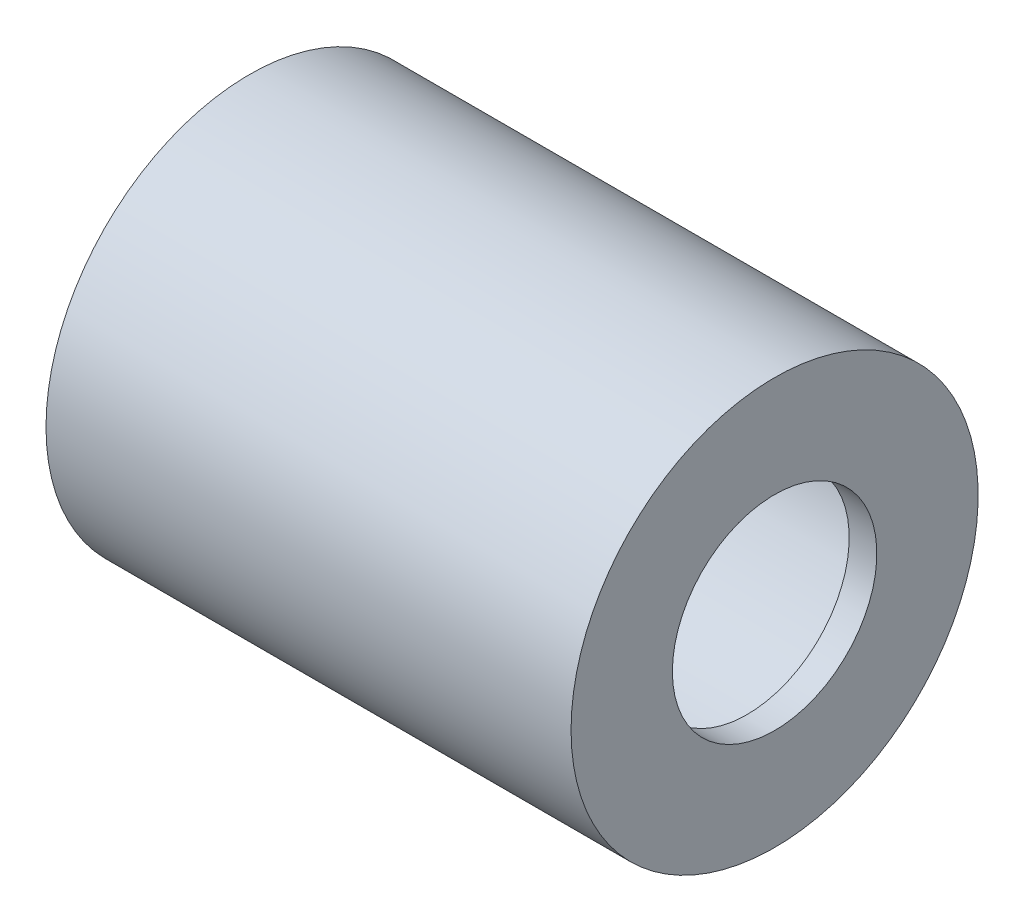
SolidWorks part; units mm, degrees
material "Copper"
ref_plane "Front Plane" through (0, 0, 0) normal (0, 0, 1) x (1, 0, 0)
ref_plane "Top Plane" through (0, 0, 0) normal (0, 1, 0) x (1, 0, 0)
ref_plane "Right Plane" through (0, 0, 0) normal (1, 0, 0) x (0, 0, -1)
sketch "Sketch1" plane through (0, 0, 0) normal (0, 0, 1) x (1, 0, 0)
  line L0 (-16.7627, -2.0938) -> (34.2373, -2.0938) construction
  line L1 (-16.7627, -2.5938) -> (-16.7627, -1.5938) construction
  line L2 (34.2373, -4.3438) -> (34.2373, 0.1562) construction
  line L3 (19.4089, -21.0938) -> (19.4089, 16.9062) construction
  line L4 (19.4089, 9.0062) -> (22.4089, 9.0062)
  line L5 (19.4089, 9.0062) -> (19.4089, 17.0062)
  line L6 (19.4089, 20.0062) -> (22.4089, 20.0062)
  line L7 (22.4089, 9.0062) -> (22.4089, 20.0062)
  line L9 (19.4089, 17.0062) -> (-34.5975, 17.0062)
  line L11 (19.4089, 20.0062) -> (-34.5975, 20.0062)
  line L12 (-34.5975, 17.0062) -> (-34.5975, 20.0062)
  dimension "D1" = 3
  dimension "D2" = 3
  dimension "D3" = 11
  dimension "D4" = 19.1
revolve "Revolve1" add sketch "Sketch1" angle 360 about L0
